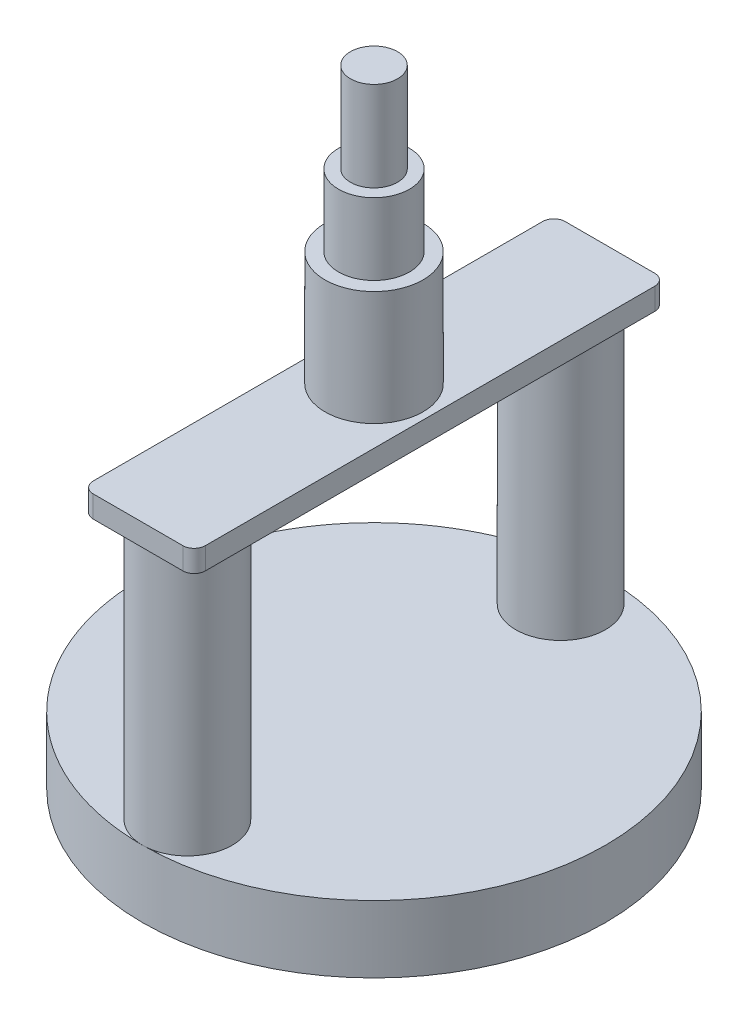
SolidWorks part; units mm, degrees
ref_plane "Front Plane" through (0, 0, 0) normal (0, 0, 1) x (1, 0, 0)
ref_plane "Top Plane" through (0, 0, 0) normal (0, 1, 0) x (1, 0, 0)
ref_plane "Right Plane" through (0, 0, 0) normal (1, 0, 0) x (0, 0, -1)
sketch "Sketch1" plane through (0, 0, 0) normal (0, 1, 0) x (1, 0, 0)
  circle A0 centre (0, 0) radius 20.65
  dimension "D1" = 41.3
extrude "Boss-Extrude1" add sketch "Sketch1" along normal blind 5.98
sketch "Sketch2" plane through (0, 5.98, 0) normal (0, 1, 0) x (1, 0, 0)
  circle A0 centre (0, -16.65) radius 4
  circle A1 centre (0, 16.65) radius 4
  circle A2 centre (0, 0) radius 20.65 construction
  dimension "D1" = 8
  dimension "D2" = 8
  dimension "D6" = 0
  dimension "D3" = 16.65
  dimension "D4" = 16.65
  dimension "D5" = 33.3
extrude "Boss-Extrude2" add sketch "Sketch2" along normal blind 23.4
sketch "Sketch3" plane through (0, 29.38, 0) normal (0, 1, 0) x (1, 0, 0)
  line L1 (-4, -21.05) -> (4, -21.05)
  line L2 (-5, -20.05) -> (-5, 20.05)
  line L3 (-4, 21.05) -> (4, 21.05)
  line L4 (5, -20.05) -> (5, 20.05)
  arc A0 (0, 20.65) -> (0, -20.65) centre (0, 0) ccw construction
  arc A1 (4, 21.05) -> (5, 20.05) centre (4, 20.05) cw
  arc A2 (-5, 20.05) -> (-4, 21.05) centre (-4, 20.05) cw
  arc A3 (4, -21.05) -> (5, -20.05) centre (4, -20.05) ccw
  arc A4 (-4, -21.05) -> (-5, -20.05) centre (-4, -20.05) cw
  point P14 (5, -21.05)
  point P17 (-5, -21.05)
  dimension "D5" = 1
  dimension "D1" = 42.1
  dimension "D2" = 21.05
  dimension "D3" = 10
  dimension "D4" = 5
extrude "Boss-Extrude3" add sketch "Sketch3" along normal blind 1.95
sketch "Sketch4" plane through (0, 31.33, 0) normal (0, 1, 0) x (1, 0, 0)
  circle A0 centre (0, 0) radius 4.375
  dimension "D1" = 8.75
extrude "Boss-Extrude4" add sketch "Sketch4" along normal blind 10.2
sketch "Sketch5" plane through (0, 41.53, 0) normal (0, 1, 0) x (1, 0, 0)
  circle A0 centre (0, 0) radius 3.165
  dimension "D1" = 6.33
extrude "Boss-Extrude5" add sketch "Sketch5" along normal blind 6.4 contours A0
sketch "Sketch6" plane through (0, 47.93, 0) normal (0, 1, 0) x (1, 0, 0)
  circle A0 centre (0, 0) radius 2.1
  dimension "D1" = 4.2
extrude "Boss-Extrude6" add sketch "Sketch6" along normal blind 8
equation "\"D3@Sketch2\"=\"D1@Sketch1\"/2-\"D2@Sketch2\"/2"
equation "\"D4@Sketch2\"=\"D3@Sketch2\""
equation "\"D2@Sketch3\"=\"D1@Sketch3\"/2"
